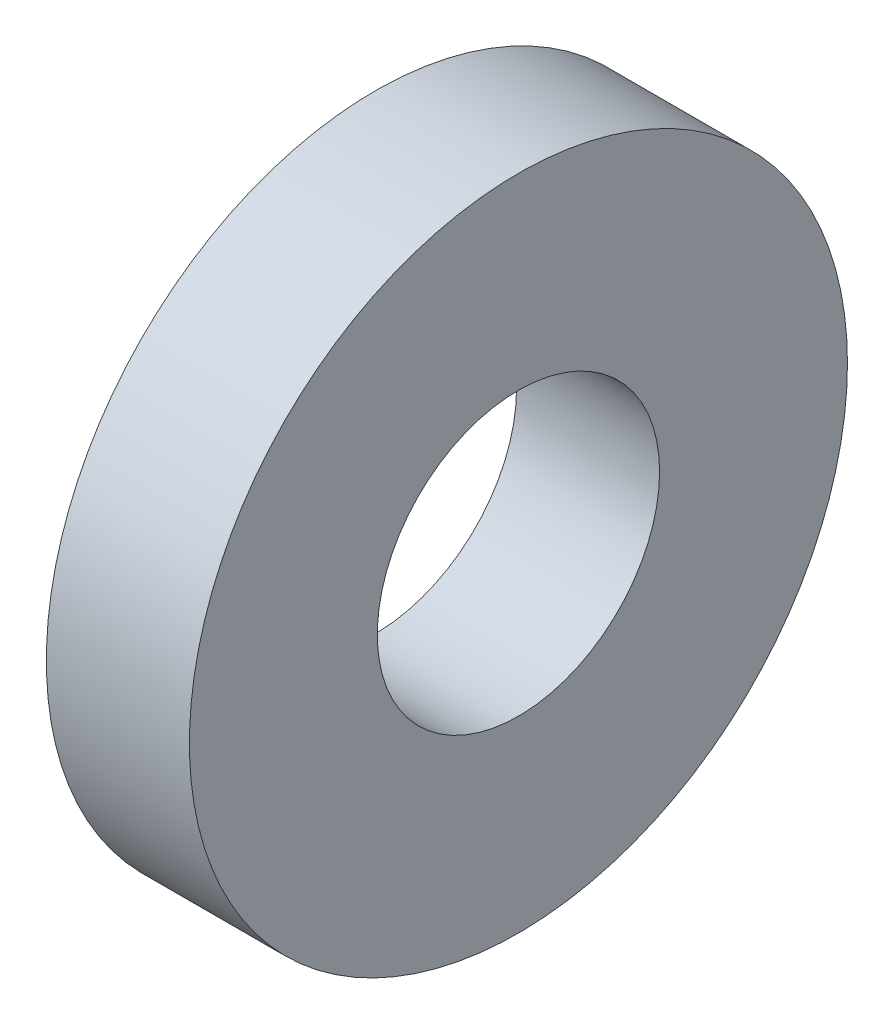
SolidWorks part; units mm, degrees
ref_plane "前视基准面" through (0, 0, 0) normal (0, 0, 1) x (1, 0, 0)
ref_plane "上视基准面" through (0, 0, 0) normal (0, 1, 0) x (1, 0, 0)
ref_plane "右视基准面" through (0, 0, 0) normal (1, 0, 0) x (0, 0, -1)
sketch "草图1" plane through (0, 0, 0) normal (1, 0, 0) x (0, 0, -1)
  circle A0 centre (0, 0) radius 3.45
  circle A1 centre (0, 0) radius 1.48
  dimension "D1" = 6.9
  dimension "D2" = 2.96
extrude "凸台-拉伸1" add sketch "草图1" along normal blind 1.5
